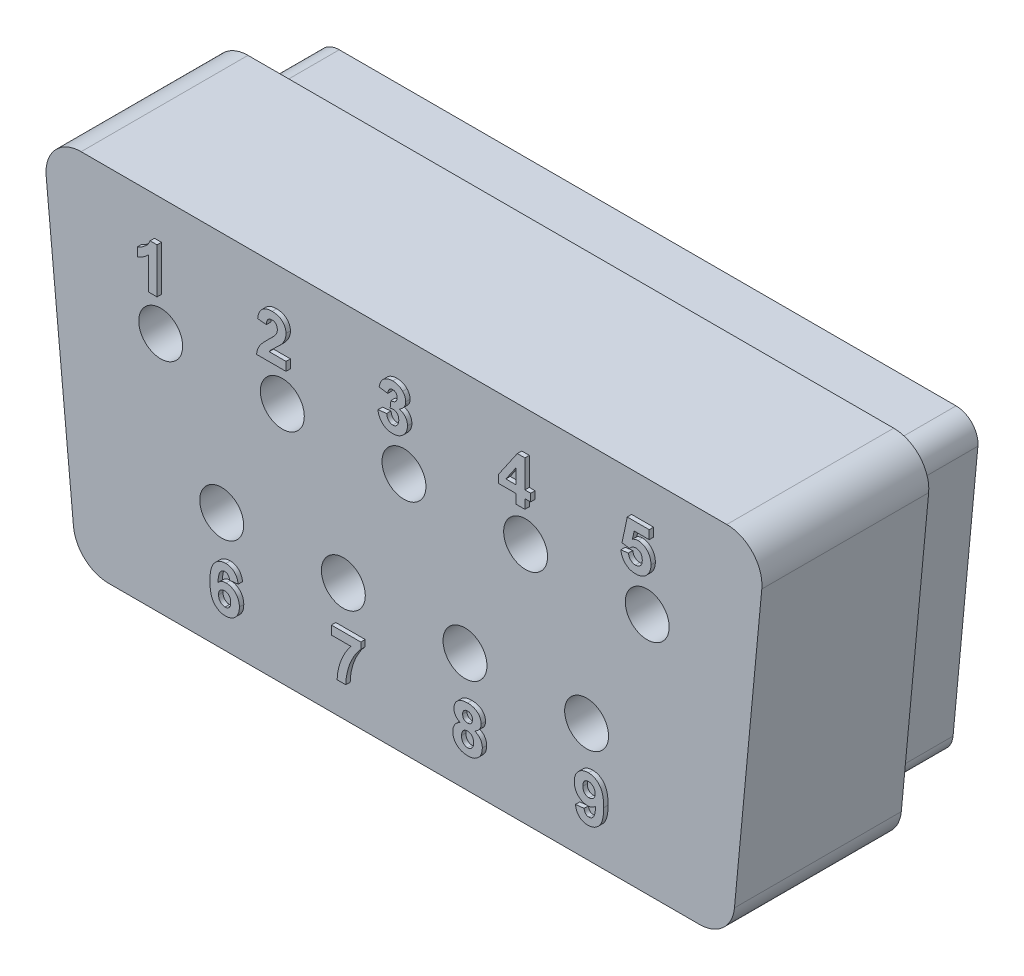
SolidWorks part; units mm, degrees
ref_plane "Front Plane" through (0, 0, 0) normal (0, 0, 1) x (1, 0, 0)
ref_plane "Top Plane" through (0, 0, 0) normal (0, 1, 0) x (1, 0, 0)
ref_plane "Right Plane" through (0, 0, 0) normal (1, 0, 0) x (0, 0, -1)
sketch "Sketch1" plane through (0, 0, 0) normal (0, 0, 1) x (1, 0, 0)
  line L0 (-7.3524, 4.1) -> (-7.3524, -7.0187) construction
  line L1 (7.3524, 4.1) -> (7.3524, -6.7915) construction
  line L4 (0, 4.1) -> (0, -4.1) construction
  line L5 (-15.42, 0) -> (15.42, 0) construction
  line L12 (7.5263, -3.3751) -> (8.1489, 3.2249)
  line L13 (-6.7298, -4.1) -> (6.7298, -4.1)
  line L14 (-8.1489, 3.2249) -> (-7.5263, -3.3751)
  line L15 (7.3524, 4.1) -> (-7.3524, 4.1)
  arc A12 (8.1489, 3.2249) -> (7.3524, 4.1) centre (7.3524, 3.3) ccw
  arc A13 (6.7298, -4.1) -> (7.5263, -3.3751) centre (6.7298, -3.3) ccw
  arc A14 (-7.5263, -3.3751) -> (-6.7298, -4.1) centre (-6.7298, -3.3) ccw
  arc A15 (-7.3524, 4.1) -> (-8.1489, 3.2249) centre (-7.3524, 3.3) ccw
  point P4 (0, 0)
  dimension "D4" = 0.8
  dimension "D1" = 16.2978
  dimension "D2" = 15.0525
  dimension "D3" = 8.2
  dimension "D5" = 4.1
  dimension "D6" = 7.5263
  dimension "D7" = 7.3524
  dimension "D8" = 5.389
  dimension "D9" = 7.3524
  dimension "D10" = 5.389
extrude "Boss-Extrude1" add sketch "Sketch1" along normal blind 3.8
sketch "Sketch2" plane through (0, 0, 0) normal (0, 0, -1) x (-1, 0, 0)
  line L0 (-9.3074, 0) -> (9.3074, 0) construction
  line L1 (0, 6.7455) -> (0, -6.1309) construction
  line L2 (-5.8958, 3.5) -> (5.8958, 3.5) construction
  line L11 (6.9289, -3.3188) -> (7.5516, 3.2812)
  line L12 (-6.7298, -3.5) -> (6.7298, -3.5)
  line L13 (7.3524, 3.5) -> (-7.3524, 3.5)
  line L14 (-7.5516, 3.2812) -> (-6.9289, -3.3188)
  line L15 (6.9546, -3.047) -> (7.5206, 2.953)
  line L16 (-6.4568, -3.5) -> (6.4568, -3.5)
  line L17 (7.0228, 3.5) -> (-7.0228, 3.5)
  line L18 (-7.5206, 2.953) -> (-6.9546, -3.047)
  arc A4 (7.5206, 2.953) -> (7.0228, 3.5) centre (7.0228, 3) ccw
  arc A5 (6.9546, -3.047) -> (6.4568, -3.5) centre (6.4568, -3) cw
  arc A6 (-6.9546, -3.047) -> (-6.4568, -3.5) centre (-6.4568, -3) ccw
  arc A7 (-7.5206, 2.953) -> (-7.0228, 3.5) centre (-7.0228, 3) cw
  arc A8 (7.5516, 3.2812) -> (7.3524, 3.5) centre (7.3524, 3.3) ccw
  arc A9 (6.7298, -3.5) -> (6.9289, -3.3188) centre (6.7298, -3.3) ccw
  arc A10 (-7.3524, 3.5) -> (-7.5516, 3.2812) centre (-7.3524, 3.3) ccw
  arc A11 (-6.9289, -3.3188) -> (-6.7298, -3.5) centre (-6.7298, -3.3) ccw
  point P2 (0, 0)
  point P8 (0, 3.5)
  dimension "D3" = 0.5
  dimension "D1" = 3.5
  dimension "D2" = 0.6
extrude "Boss-Extrude2" add sketch "Sketch2" along normal blind 1.75
sketch "Sketch3" plane through (0, 0, -1.75) normal (0, 0, -1) x (-1, 0, 0)
  line L0 (-7.8447, 0) -> (7.8447, 0) construction
  line L1 (-7.5263, -3.3751) -> (-8.1489, 3.2249) construction
  line L2 (8.1489, 3.2249) -> (7.5263, -3.3751) construction
  line L3 (7.5206, 2.953) -> (7.5206, -6.4358) construction
  line L4 (-7.5206, 2.953) -> (-7.5206, -5.6245) construction
  line L5 (2.77, 1.42) -> (5.54, 1.42) construction
  line L6 (4.155, 1.42) -> (4.155, -5.9419) construction
  circle A0 centre (5.54, 1.42) radius 0.5
  circle A1 centre (2.77, 1.42) radius 0.5
  circle A2 centre (0, 1.42) radius 0.5
  circle A3 centre (-2.77, 1.42) radius 0.5
  circle A4 centre (-5.54, 1.42) radius 0.5
  circle A5 centre (4.1506, -1.42) radius 0.5
  circle A6 centre (1.3806, -1.42) radius 0.5
  circle A7 centre (-1.3894, -1.42) radius 0.5
  circle A8 centre (-4.1594, -1.42) radius 0.5
  dimension "D2" = 1
  dimension "D14" = 1
  dimension "D1" = 1.9806
  dimension "D3" = 1.42
  dimension "D5" = 2.77
  dimension "D6" = 2.77
  dimension "D7" = 2.77
  dimension "D8" = 2.77
  dimension "D9" = 1.9806
  dimension "D10" = 3.3656
  dimension "D11" = 3.37
  dimension "D12" = 4
  dimension "D13" = 1.42
  dimension "D15" = 1.42
  dimension "D4" = 5
extrude "Cut-Extrude1" cut sketch "Sketch3" against normal up to surface (5.55 mm away) up to face at (0, -0.0321, 3.8)
sketch "Sketch4" plane through (0, 0, 3.8) normal (0, 0, 1) x (1, 0, 0)
  line L0 (-8.0522, 2.2) -> (8.0522, 2.2) construction
  line L1 (-8.1489, 3.2249) -> (-7.5263, -3.3751) construction
  line L2 (7.5263, -3.3751) -> (8.1489, 3.2249) construction
  line L3 (7.3524, 4.1) -> (-7.3524, 4.1) construction
  line L4 (-7.5334, -3.3) -> (7.5334, -3.3) construction
  line L5 (-6.7298, -4.1) -> (6.7298, -4.1) construction
  text T0 "     1     2     3     4     5 " font "Arial" height in points 4
  text T1 "        6     7     8     9" font "Arial" height in points 4
  dimension "D1" = 1.9
  dimension "D2" = 0.8
extrude "Boss-Extrude3" add sketch "Sketch4" along normal blind 0.1
sketch "Sketch6" plane through (0, 0, -1.75) normal (0, 0, -1) x (-1, 0, 0)
  line L0 (-7.4543, 2.25) -> (7.4543, 2.25) construction
  line L1 (-7.5206, 2.953) -> (-6.9546, -3.047) construction
  line L2 (6.9546, -3.047) -> (7.5206, 2.953) construction
  line L3 (7.0228, 3.5) -> (-7.0228, 3.5) construction
  line L4 (-6.9307, -3.3) -> (6.9307, -3.3) construction
  line L5 (-7.5206, 2.953) -> (-6.9546, -3.047) construction
  line L6 (-6.4568, -3.5) -> (6.4568, -3.5) construction
  text T0 "    5     4     3     2     1" font "Arial" height in points 4
  text T1 "      9     8     7     6" font "Arial" height in points 4
  dimension "D1" = 1.25
  dimension "D2" = 0.2
extrude "Boss-Extrude4" add sketch "Sketch6" along normal blind 0.1
ref_plane "Plane2" through (0, 0, 2.05) normal (0, 0, 1) x (1, 0, 0)
sketch "Sketch8" plane through (0, 0, 2.05) normal (0, 0, 1) x (1, 0, 0)
  circle A0 centre (-5.54, 1.42) radius 0.75
  circle A1 centre (-2.77, 1.42) radius 0.75
  circle A2 centre (0, 1.42) radius 0.75
  circle A3 centre (2.77, 1.42) radius 0.75
  circle A4 centre (5.54, 1.42) radius 0.75
  circle A5 centre (4.1594, -1.42) radius 0.75
  circle A6 centre (1.3894, -1.42) radius 0.75
  circle A7 centre (-1.3806, -1.42) radius 0.75
  circle A8 centre (-4.1506, -1.42) radius 0.75
  dimension "D1" = 1.5
extrude "Cut-Extrude3" cut sketch "Sketch8" against normal up to surface (3.8 mm away) up to face at (-4.1534, -2.7019, -1.75)
